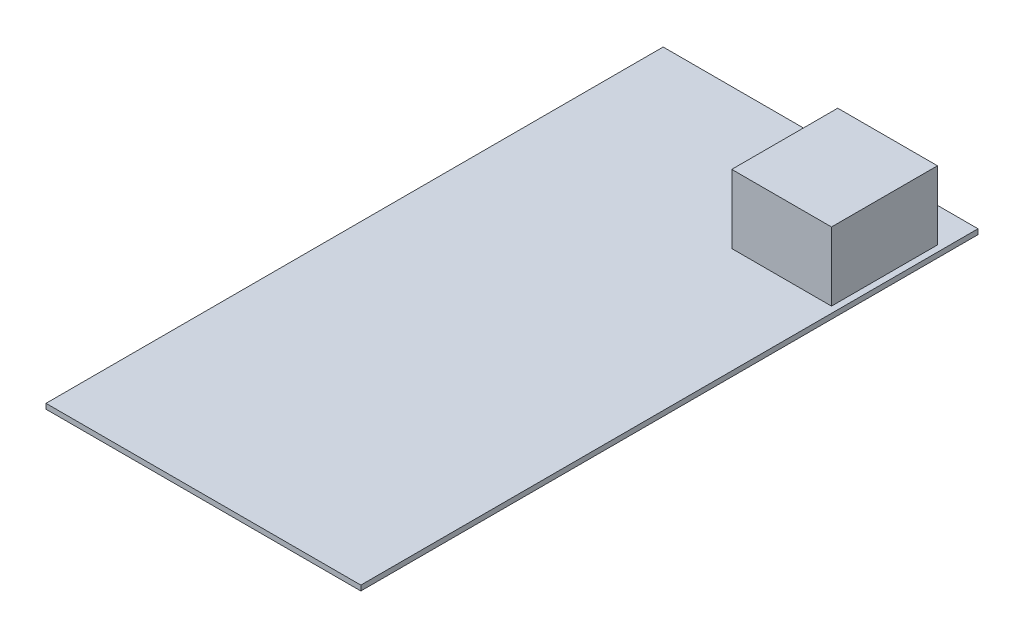
SolidWorks part; units mm, degrees
ref_plane "Front Plane" through (0, 0, 0) normal (0, 0, 1) x (1, 0, 0)
ref_plane "Top Plane" through (0, 0, 0) normal (0, 1, 0) x (1, 0, 0)
ref_plane "Right Plane" through (0, 0, 0) normal (1, 0, 0) x (0, 0, -1)
sketch "Sketch1" plane through (0, 0, 0) normal (0, 1, 0) x (1, 0, 0)
  line L1 (-50.5, 99) -> (50.5, 99)
  line L2 (-50.5, 99) -> (-50.5, -99)
  line L3 (-50.5, -99) -> (50.5, -99)
  line L4 (50.5, 99) -> (50.5, -99)
  line L5 (-50.5, 99) -> (50.5, -99) construction
  line L6 (-50.5, -99) -> (50.5, 99) construction
  point P0 (0, 0)
  dimension "D1" = 101
  dimension "D2" = 198
extrude "HV Board" add sketch "Sketch1" along normal blind 1.65
sketch "Sketch2" plane through (0, 1.65, 0) normal (0, 1, 0) x (1, 0, 0)
  line L0 (50.5, 99) -> (-50.5, 99) construction
  line L1 (16.5, 88) -> (48.5, 88)
  line L2 (16.5, 88) -> (16.5, 54)
  line L3 (16.5, 54) -> (48.5, 54)
  line L4 (48.5, 88) -> (48.5, 54)
  line L5 (50.5, -99) -> (50.5, 99) construction
  dimension "D1" = 34
  dimension "D2" = 32
  dimension "D3" = 11
  dimension "D4" = 2
extrude "Inductor" add sketch "Sketch2" along normal blind 22
